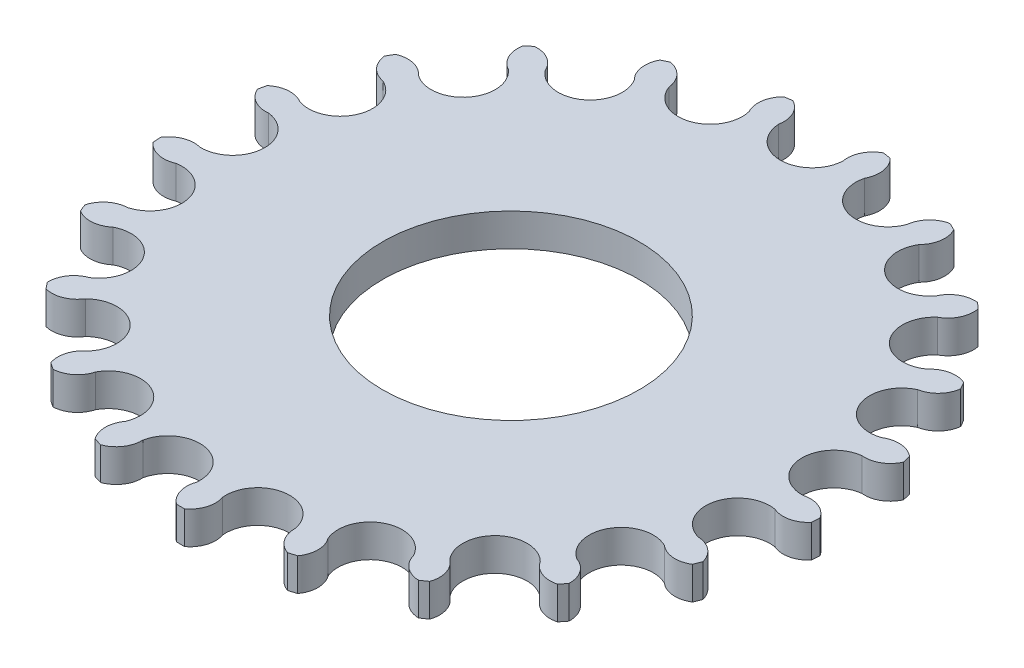
SolidWorks part; units mm, degrees
ref_plane "Front Plane" through (0, 0, 0) normal (0, 0, 1) x (1, 0, 0)
ref_plane "Top Plane" through (0, 0, 0) normal (0, 1, 0) x (1, 0, 0)
ref_plane "Right Plane" through (0, 0, 0) normal (1, 0, 0) x (0, 0, -1)
sketch "Sketch1" plane through (0, 0, 0) normal (0, 1, 0) x (1, 0, 0)
  line L0 (23.5, 0) -> (0.5, 0) construction
  line L1 (0, 0) -> (0, 26) construction
  circle A0 centre (0, 0) radius 23.5 construction
  arc A1 (-2.4965, 23.367) -> (2.4965, 23.367) centre (0, 23.5) ccw
  circle A2 centre (-6.5, 0) radius 3
  circle A3 centre (0, 7) radius 3
  circle A4 centre (7, 0) radius 3
  circle A5 centre (0, -7) radius 3
  circle A6 centre (0, 0) radius 21 construction
  circle A7 centre (0, 0) radius 26 construction
  arc A8 (2.4965, 23.367) -> (3.5246, 25.5076) centre (4.4613, 23.7406) cw
  arc A9 (-2.4965, 23.367) -> (-3.5246, 25.5076) centre (-4.4613, 23.7406) ccw
  arc A10 (4.502, 23.0647) -> (4.1505, 25.4133) centre (2.7346, 24.0008) ccw
  arc A11 (4.502, 23.0647) -> (9.2731, 21.593) centre (6.9267, 22.456) ccw
  arc A12 (9.2731, 21.593) -> (10.8865, 23.3355) centre (11.2607, 21.3709) cw
  arc A13 (11.1004, 20.713) -> (11.4568, 23.0609) centre (9.6875, 22.1285) ccw
  arc A14 (11.1004, 20.713) -> (15.2258, 17.9004) centre (13.238, 19.4166) ccw
  arc A15 (15.2258, 17.9004) -> (17.2811, 19.09) centre (17.0596, 17.1023) cw
  arc A16 (16.7126, 16.5209) -> (17.7452, 18.6594) centre (15.7796, 18.29) ccw
  arc A17 (16.7126, 16.5209) -> (19.8256, 12.6173) centre (18.373, 14.652) ccw
  arc A18 (19.8256, 12.6173) -> (22.1402, 13.1481) centre (21.3427, 11.314) cw
  arc A19 (20.8397, 10.8608) -> (22.4567, 12.5999) centre (20.4696, 12.8263) ccw
  arc A20 (20.8397, 10.8608) -> (22.6638, 6.213) centre (21.8755, 8.5855) ccw
  arc A21 (22.6638, 6.213) -> (25.0321, 6.0381) centre (23.7294, 4.5205) cw
  arc A22 (23.1151, 4.2357) -> (25.1729, 5.4209) centre (23.3408, 6.2229) ccw
  arc A23 (23.1151, 4.2357) -> (23.4882, -0.7433) centre (23.4343, 1.7562) ccw
  arc A24 (23.4882, -0.7433) -> (25.6997, -1.6085) centre (24.0076, -2.6747) cw
  arc A25 (23.3367, -2.7658) -> (25.6524, -2.2398) centre (24.1381, -0.9334) ccw
  arc A26 (23.3367, -2.7658) -> (22.2256, -7.6335) centre (22.9108, -5.2292) ccw
  arc A27 (22.2256, -7.6335) -> (24.0838, -9.1122) centre (22.1526, -9.6322) cw
  arc A28 (21.4847, -9.5215) -> (23.8525, -9.7015) centre (22.7906, -8.0067) ccw
  arc A29 (21.4847, -9.5215) -> (18.9882, -13.8455) centre (20.3516, -11.75) ccw
  arc A30 (18.9882, -13.8455) -> (20.328, -15.8062) centre (18.3293, -15.7339) cw
  arc A31 (17.7236, -15.4312) -> (19.9333, -16.3011) centre (19.418, -14.3686) ccw
  arc A32 (17.7236, -15.4312) -> (14.0636, -18.8273) centre (15.9841, -17.2267) ccw
  arc A33 (14.0636, -18.8273) -> (14.7659, -21.0957) centre (12.8773, -20.4375) cw
  arc A34 (12.3878, -19.9698) -> (14.2429, -21.4523) centre (14.3201, -19.4538) ccw
  arc A35 (12.3878, -19.9698) -> (7.8893, -22.1361) centre (10.1963, -21.1728) ccw
  arc A36 (7.8893, -22.1361) -> (7.8918, -24.5108) centre (6.2812, -23.3252) cw
  arc A37 (5.9513, -22.734) -> (7.2869, -24.6974) centre (7.9498, -22.8105) ccw
  arc A38 (5.9513, -22.734) -> (1.0141, -23.4781) centre (3.5025, -23.2375) ccw
  arc A39 (1.0141, -23.4781) -> (0.3165, -25.7481) centre (-0.8731, -24.1403) cw
  arc A40 (-1.0141, -23.4781) -> (-0.3165, -25.7481) centre (0.8731, -24.1403) ccw
  arc A41 (-1.0141, -23.4781) -> (-5.9513, -22.734) centre (-3.5025, -23.2375) ccw
  arc A42 (-5.9513, -22.734) -> (-7.2869, -24.6974) centre (-7.9498, -22.8105) cw
  arc A43 (-7.8893, -22.1361) -> (-7.8918, -24.5108) centre (-6.2812, -23.3252) ccw
  arc A44 (-7.8893, -22.1361) -> (-12.3878, -19.9698) centre (-10.1963, -21.1728) ccw
  arc A45 (-12.3878, -19.9698) -> (-14.2429, -21.4523) centre (-14.3201, -19.4538) cw
  arc A46 (-14.0636, -18.8273) -> (-14.7659, -21.0957) centre (-12.8773, -20.4375) ccw
  arc A47 (-14.0636, -18.8273) -> (-17.7236, -15.4312) centre (-15.9841, -17.2267) ccw
  arc A48 (-17.7236, -15.4312) -> (-19.9333, -16.3011) centre (-19.418, -14.3686) cw
  arc A49 (-18.9882, -13.8455) -> (-20.328, -15.8062) centre (-18.3293, -15.7339) ccw
  arc A50 (-18.9882, -13.8455) -> (-21.4847, -9.5215) centre (-20.3516, -11.75) ccw
  arc A51 (-21.4847, -9.5215) -> (-23.8525, -9.7015) centre (-22.7906, -8.0067) cw
  arc A52 (-22.2256, -7.6335) -> (-24.0838, -9.1122) centre (-22.1526, -9.6322) ccw
  arc A53 (-22.2256, -7.6335) -> (-23.3367, -2.7658) centre (-22.9108, -5.2292) ccw
  arc A54 (-23.3367, -2.7658) -> (-25.6524, -2.2398) centre (-24.1381, -0.9334) cw
  arc A55 (-23.4882, -0.7433) -> (-25.6997, -1.6085) centre (-24.0076, -2.6747) ccw
  arc A56 (-23.4882, -0.7433) -> (-23.1151, 4.2357) centre (-23.4343, 1.7562) ccw
  arc A57 (-23.1151, 4.2357) -> (-25.1729, 5.4209) centre (-23.3408, 6.2229) cw
  arc A58 (-22.6638, 6.213) -> (-25.0321, 6.0381) centre (-23.7294, 4.5205) ccw
  arc A59 (-22.6638, 6.213) -> (-20.8397, 10.8608) centre (-21.8755, 8.5855) ccw
  arc A60 (-20.8397, 10.8608) -> (-22.4567, 12.5999) centre (-20.4696, 12.8263) cw
  arc A61 (-19.8256, 12.6173) -> (-22.1402, 13.1481) centre (-21.3427, 11.314) ccw
  arc A62 (-19.8256, 12.6173) -> (-16.7126, 16.5209) centre (-18.373, 14.652) ccw
  arc A63 (-16.7126, 16.5209) -> (-17.7452, 18.6594) centre (-15.7796, 18.29) cw
  arc A64 (-15.2258, 17.9004) -> (-17.2811, 19.09) centre (-17.0596, 17.1023) ccw
  arc A65 (-15.2258, 17.9004) -> (-11.1004, 20.713) centre (-13.238, 19.4166) ccw
  arc A66 (-11.1004, 20.713) -> (-11.4568, 23.0609) centre (-9.6875, 22.1285) cw
  arc A67 (-9.2731, 21.593) -> (-10.8865, 23.3355) centre (-11.2607, 21.3709) ccw
  arc A68 (-9.2731, 21.593) -> (-4.502, 23.0647) centre (-6.9267, 22.456) ccw
  arc A69 (-4.502, 23.0647) -> (-4.1505, 25.4133) centre (-2.7346, 24.0008) cw
  arc A70 (-10.8865, 23.3355) -> (-11.4568, 23.0609) centre (0, 0) ccw
  arc A71 (-17.2811, 19.09) -> (-17.7452, 18.6594) centre (0, 0) ccw
  arc A72 (-22.1402, 13.1481) -> (-22.4567, 12.5999) centre (0, 0) ccw
  arc A73 (-25.0321, 6.0381) -> (-25.1729, 5.4209) centre (0, 0) ccw
  arc A74 (-25.6997, -1.6085) -> (-25.6524, -2.2398) centre (0, 0) ccw
  arc A75 (-24.0838, -9.1122) -> (-23.8525, -9.7015) centre (0, 0) ccw
  arc A76 (-20.328, -15.8062) -> (-19.9333, -16.3011) centre (0, 0) ccw
  arc A77 (-14.7659, -21.0957) -> (-14.2429, -21.4523) centre (0, 0) ccw
  arc A78 (-7.8918, -24.5108) -> (-7.2869, -24.6974) centre (0, 0) ccw
  arc A79 (-0.3165, -25.7481) -> (0.3165, -25.7481) centre (0, 0) ccw
  arc A80 (7.2869, -24.6974) -> (7.8918, -24.5108) centre (0, 0) ccw
  arc A81 (14.2429, -21.4523) -> (14.7659, -21.0957) centre (0, 0) ccw
  arc A82 (19.9333, -16.3011) -> (20.328, -15.8062) centre (0, 0) ccw
  arc A83 (23.8525, -9.7015) -> (24.0838, -9.1122) centre (0, 0) ccw
  arc A84 (25.6524, -2.2398) -> (25.6997, -1.6085) centre (0, 0) ccw
  arc A85 (25.1729, 5.4209) -> (25.0321, 6.0381) centre (0, 0) ccw
  arc A86 (22.4567, 12.5999) -> (22.1402, 13.1481) centre (0, 0) ccw
  arc A87 (17.7452, 18.6594) -> (17.2811, 19.09) centre (0, 0) ccw
  arc A88 (11.4568, 23.0609) -> (10.8865, 23.3355) centre (0, 0) ccw
  arc A89 (4.1505, 25.4133) -> (3.5246, 25.5076) centre (0, 0) ccw
  arc A90 (-3.5246, 25.5076) -> (-4.1505, 25.4133) centre (0, 0) ccw
  point P16 (0.5, 0)
  point P167 (0, 0)
  dimension "D1" = 47
  dimension "D4" = 6
  dimension "D8" = 52
  dimension "D9" = 42
  dimension "D10" = 2
  dimension "D11" = 51.5
  dimension "D2" = 23
  dimension "D3" = 7
  dimension "D5" = 7
  dimension "D6" = 7
  dimension "D7" = 7
  dimension "D12" = 21
  dimension "D13" = 0.3165
extrude "Boss-Extrude1" add sketch "Sketch1" along normal blind 2.55
ref_plane "Plane1" through (0, 1.275, 0) normal (0, 1, 0) x (1, 0, 0)
sketch "Sketch2" plane through (0, 1.275, 0) normal (0, 1, 0) x (1, 0, 0)
  circle A0 centre (0, 0) radius 10
  dimension "D1" = 20
extrude "Cut-Extrude1" cut sketch "Sketch2" against normal blind 4 and the other way blind 4
